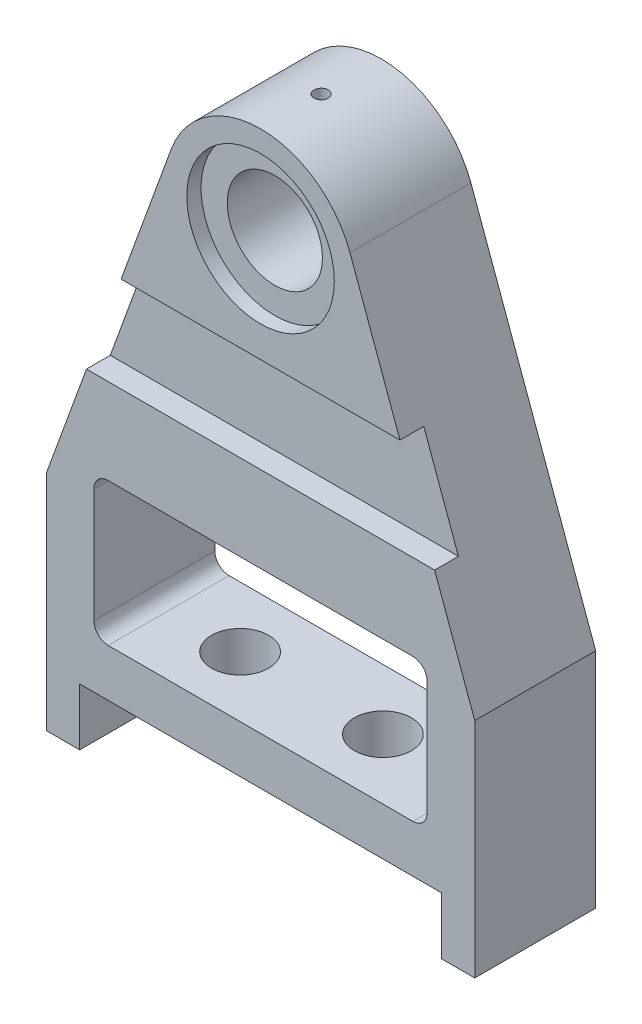
SolidWorks part; units mm, degrees
material "Beryllium"
ref_plane "Front Plane" through (0, 0, 0) normal (0, 0, 1) x (1, 0, 0)
ref_plane "Top Plane" through (0, 0, 0) normal (0, 1, 0) x (1, 0, 0)
ref_plane "Right Plane" through (0, 0, 0) normal (1, 0, 0) x (0, 0, -1)
sketch "Sketch1" plane through (0, 0, 0) normal (0, 0, 1) x (1, 0, 0)
  line L0 (-38, 0) -> (38, 0)
  line L1 (-38, 0) -> (-38, -12)
  line L2 (-38, -12) -> (-45, -12)
  line L3 (-45, -12) -> (-45, 34.8396)
  line L4 (-45, 34.8396) -> (-18.7939, 106.8404)
  line L5 (18.7939, 106.8404) -> (45, 34.8396)
  line L6 (45, 34.8396) -> (45, -12)
  line L7 (45, -12) -> (38, -12)
  line L8 (38, -12) -> (38, 0)
  line L9 (0, 100) -> (0, 0) construction
  arc A0 (-18.7939, 106.8404) -> (18.7939, 106.8404) centre (0, 100) cw
  circle A1 centre (0, 100) radius 10
  dimension "D4" = 20
  dimension "D5" = 20
  dimension "D1" = 76
  dimension "D2" = 90
  dimension "D3" = 12
  dimension "D6" = 100
extrude "Extrude1" add sketch "Sketch1" along normal blind 25.4
sketch "Sketch2" plane through (0, 0, 25.4) normal (0, 0, 1) x (1, 0, 0)
  line L0 (-38, 0) -> (38, 0) construction
  line L1 (-32, 10) -> (32, 10)
  line L2 (-35, 13) -> (-35, 37)
  line L3 (-32, 40) -> (32, 40)
  line L4 (35, 13) -> (35, 37)
  line L5 (0, 10) -> (0, 0) construction
  arc A0 (-35, 37) -> (-32, 40) centre (-32, 37) cw
  arc A1 (32, 40) -> (35, 37) centre (32, 37) cw
  arc A2 (-32, 10) -> (-35, 13) centre (-32, 13) cw
  arc A3 (32, 10) -> (35, 13) centre (32, 13) ccw
  point P13 (35, 40)
  point P18 (35, 10)
  dimension "D3" = 3
  dimension "D4" = 3
  dimension "D1" = 10
  dimension "D2" = 30
  dimension "D5" = 70
extrude "Cut-Extrude1" cut sketch "Sketch2" against normal through all
sketch "Sketch5" plane through (0, 0, 0) normal (0, -1, 0) x (1, 0, 0)
  line L0 (-38, 12.7) -> (38, 12.7) construction
  line L2 (-38, 25.4) -> (-38, 0) construction
  line L3 (38, 25.4) -> (38, 0) construction
  circle A0 centre (13, 12.7) radius 6
  circle A1 centre (-17, 12.7) radius 6
  dimension "D1" = 12
  dimension "D2" = 30
  dimension "D3" = 25
extrude "Cut-Extrude2" cut sketch "Sketch5" against normal up to next
ref_plane "Plane1" through (0, 137, 0) normal (0, 1, 0) x (-1, 0, 0)
sketch "Sketch6" plane through (0, 137, 0) normal (0, 1, 0) x (-1, 0, 0)
  line L0 (38, 25.4) -> (38, 0) construction
  line L1 (38, 25.4) -> (38, 0) construction
  line L2 (-38, 25.4) -> (-38, 0) construction
  line L3 (-38, 25.4) -> (-38, 0) construction
  line L4 (38, 0) -> (-38, 25.4) construction
  circle A0 centre (0, 12.7) radius 1.5
  dimension "D1" = 3
extrude "Cut-Extrude3" cut sketch "Sketch6" against normal up to surface (27.1131 mm away)
sketch "Sketch7" plane through (0, 0, 25.4) normal (0, 0, 1) x (1, 0, 0)
  line L0 (32, 40) -> (-32, 40) construction
  line L1 (-63.2444, 58) -> (67.8459, 58)
  line L2 (-63.2444, 58) -> (-63.2444, 78)
  line L3 (-63.2444, 78) -> (67.8459, 78)
  line L4 (67.8459, 58) -> (67.8459, 78)
  dimension "D1" = 20
  dimension "D2" = 18
extrude "Extrude2" cut sketch "Sketch7" against normal blind 5
sketch "Sketch8" plane through (0, 0, 25.4) normal (0, 0, 1) x (1, 0, 0)
  circle A0 centre (0, 100) radius 15.5
  circle A1 centre (0, 100) radius 10 construction
  circle A2 centre (0, 100) radius 10
  dimension "D1" = 31
extrude "Extrude3" cut sketch "Sketch8" against normal blind 3
ref_plane "Plane2" through (0, 0, 12.7) normal (0, 0, 1) x (1, 0, 0)
mirror "Mirror1" about plane through (0, 0, 12.7) normal (0, 0, 1) of "Extrude3"
